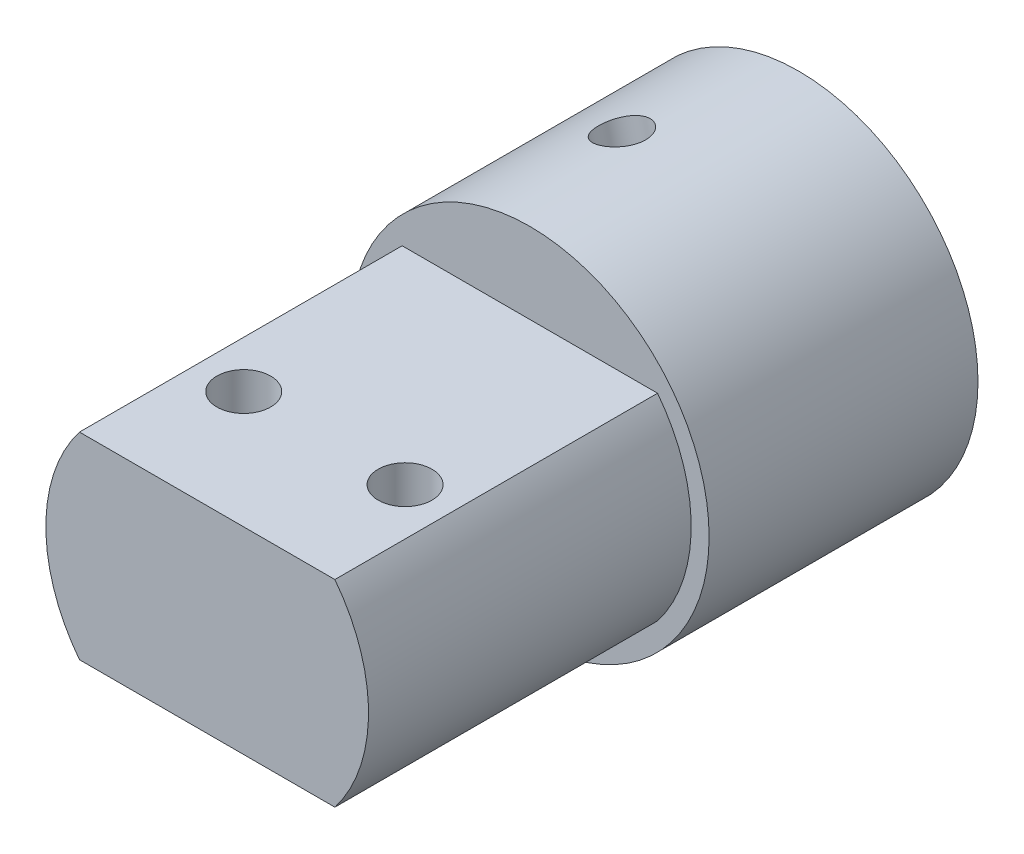
SolidWorks part; units mm, degrees
ref_plane "前视基准面" through (0, 0, 0) normal (0, 0, 1) x (1, 0, 0)
ref_plane "上视基准面" through (0, 0, 0) normal (0, 1, 0) x (1, 0, 0)
ref_plane "右视基准面" through (0, 0, 0) normal (1, 0, 0) x (0, 0, -1)
sketch "草图1" plane through (0, 0, 0) normal (0, 0, 1) x (1, 0, 0)
  line L0 (-11.4891, -8) -> (11.4891, -8)
  arc A0 (11.4891, -8) -> (-11.4891, -8) centre (0, 0) ccw
  circle A1 centre (0, 0) radius 5.25
  dimension "D1" = 28
  dimension "D3" = 10.5
  dimension "D2" = 8
extrude "凸台-拉伸1" add sketch "草图1" along normal blind 15
sketch "草图2" plane through (0, 0, 15) normal (0, 0, 1) x (1, 0, 0)
  line L0 (-13.4164, 4) -> (13.4164, 4)
  line L1 (-11.4891, -8) -> (11.4891, -8) construction
  arc A0 (11.4891, -8) -> (-11.4891, -8) centre (0, 0) ccw construction
  arc A1 (13.4164, 4) -> (-13.4164, 4) centre (0, 0) ccw
  dimension "D1" = 12
extrude "切除-拉伸1" cut sketch "草图2" against normal blind 10
sketch "草图3" plane through (0, 0, 15) normal (0, 0, 1) x (1, 0, 0)
  line L0 (-13.4164, 4) -> (-3.4004, 4) construction
  line L1 (-13.4164, 4) -> (-3.4004, 4) construction
  line L2 (-7.1239, 5.5) -> (7.1239, 5.5)
  line L3 (-7.1239, -5.5) -> (7.1239, -5.5)
  line L4 (-16.2067, 0) -> (21.8127, 0) construction
  line L6 (-16.2067, 5.5) -> (21.8127, 5.5) construction
  line L7 (-16.2067, -5.5) -> (21.8127, -5.5) construction
  arc A0 (-7.1239, 5.5) -> (-7.1239, -5.5) centre (0, 0) ccw
  arc A1 (7.1239, -5.5) -> (7.1239, 5.5) centre (0, 0) ccw
  dimension "D4" = 18
  dimension "D1" = 1.5
  dimension "D2" = 11
  dimension "D3" = 5.5
extrude "凸台-拉伸2" add sketch "草图3" along normal blind 18
sketch "草图4" plane through (0, 5.5, 0) normal (0, 1, 0) x (1, 0, 0)
  line L0 (0, 10.497) -> (0, -50.4006) construction
  line L1 (7.1239, -33) -> (-7.1239, -33) construction
  circle A0 centre (4.5, -26.46) radius 1.5
  circle A1 centre (-4.5, -26.46) radius 1.5
  dimension "D1" = 3
  dimension "D2" = 4.5
  dimension "D3" = 6.54
extrude "切除-拉伸2" cut sketch "草图4" against normal through all
sketch "草图5" plane through (0, 0, 0) normal (0, 0, -1) x (-1, 0, 0)
  circle A0 centre (0, 0) radius 5.25
  circle A1 centre (0, 0) radius 14
extrude "凸台-拉伸3" add sketch "草图5" against normal blind 15
sketch "草图6" plane through (0, 0, 0) normal (0, 0, -1) x (-1, 0, 0)
  circle A0 centre (0, 0) radius 10
  circle A1 centre (0, 0) radius 18.0436
  dimension "D1" = 20
extrude "切除-拉伸3" cut sketch "草图6" against normal blind 15
sketch "草图7" plane through (0, 0, 0) normal (0, 0, -1) x (-1, 0, 0)
  line L0 (-1.9853, 4.589) -> (3.8495, 3.1908)
  line L2 (3.8495, 3.1908) -> (-1.9853, 4.589) construction
  arc A0 (-1.9853, 4.589) -> (3.8495, 3.1908) centre (0, 0) ccw
  circle A1 centre (0, 0) radius 6.9865
  dimension "D1" = 10
  dimension "D2" = 0
extrude "凸台-拉伸4" add sketch "草图7" against normal blind 15
sketch "草图8" plane through (-0.9321, 3.8899, 0) normal (0.233, -0.9725, 0) x (0.9725, 0.233, 0)
  circle A0 centre (0, 7.5443) radius 1.35
  dimension "D1" = 2.7
extrude "切除-拉伸4" cut sketch "草图8" against normal blind 15
